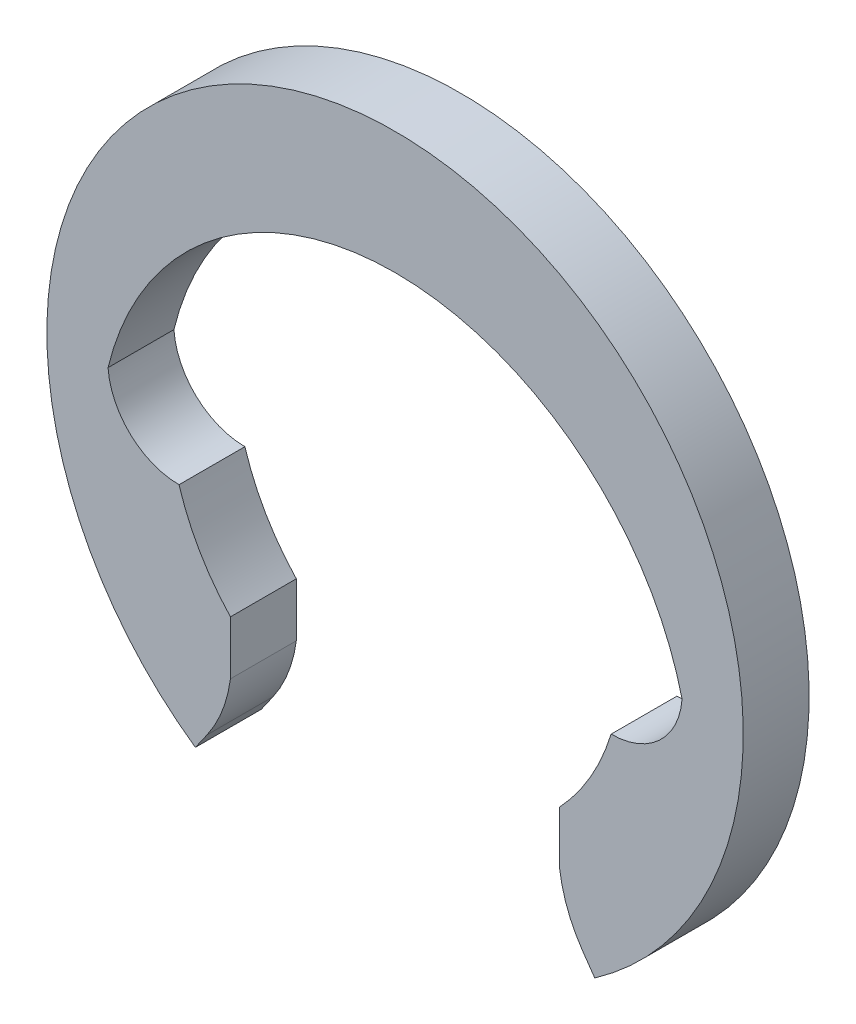
SolidWorks part; units mm, degrees
ref_plane "Front" through (0, 0, 0) normal (0, 0, 1) x (1, 0, 0)
ref_plane "Top" through (0, 0, 0) normal (0, 1, 0) x (1, 0, 0)
ref_plane "Right" through (0, 0, 0) normal (1, 0, 0) x (0, 0, -1)
sketch "Layout" plane through (0, 0, 0) normal (0, 0, 1) x (1, 0, 0)
  line L0 (0, 3.7) -> (0, -3.7) construction
  line L1 (-2.4, 0) -> (-3.7, 0) construction
  line L2 (-3.7, 0) -> (-4.4, 0) construction
  line L3 (-2.4, 0) -> (2.4, 0) construction
  line L4 (-1.7494, -2.4984) -> (-1.7494, -1.643) construction
  line L5 (-2.2956, -0.7) -> (2.2956, -0.7) construction
  line L6 (-2.4, 0) -> (-2.4, -0.7) construction
  line L7 (0, 0) -> (-1.3766, -1.966) construction
  line L8 (-1.3766, -1.966) -> (-2.1222, -3.0309) construction
  circle A0 centre (0, 0) radius 3.7 construction
  circle A1 centre (0, 0) radius 2.4 construction
  arc A2 (0, 2.4) -> (-3.05, 0) centre (0, -0.738) ccw construction
  circle A3 centre (0, 0) radius 3.8 construction
  arc A4 (-3.05, 0) -> (-2.2956, -0.7) centre (-2.2956, 0.0565) ccw construction
  dimension "D1" = 35
sketch "Sketch2" plane through (0, 0, 0) normal (0, 0, 1) x (1, 0, 0)
  line L0 (-1.7494, -2.4984) -> (-1.7494, -2.2133) construction
  line L1 (-1.7494, -2.2133) -> (-1.7494, -1.9282)
  line L2 (-1.7494, -1.9282) -> (-1.7494, -1.643)
  line L4 (0, 3.7) -> (0, -3.7) construction
  line L5 (-1.7494, -2.4984) -> (-1.8737, -2.6759) construction
  line L6 (0, 3.7) -> (0, 2.4) construction
  line L7 (-1.8737, -2.6759) -> (-1.998, -2.8534) construction
  line L8 (-1.998, -2.8534) -> (-2.1222, -3.0309)
  line L9 (-1.3766, -1.966) -> (-2.1222, -3.0309) construction
  line L10 (1.7494, -1.9282) -> (1.7494, -1.643)
  line L11 (1.7494, -2.2133) -> (1.7494, -1.9282)
  line L12 (1.998, -2.8534) -> (2.1222, -3.0309)
  circle A0 centre (0, 0) radius 3.7 construction
  arc A1 (0, 2.4) -> (-3.05, 0) centre (0, -0.738) ccw construction
  arc A2 (-3.05, 0) -> (-2.2956, -0.7) centre (-2.2956, 0.0565) ccw construction
  circle A3 centre (0, 0) radius 2.4 construction
  arc A4 (2.1222, -3.0309) -> (-2.1222, -3.0309) centre (0, 0) ccw
  arc A5 (3.05, 0) -> (-3.05, 0) centre (0, -0.738) ccw
  arc A6 (-3.05, 0) -> (-2.2956, -0.7) centre (-2.2956, 0.0565) ccw
  arc A7 (-2.2956, -0.7) -> (-1.7494, -1.643) centre (0, 0) ccw
  arc A8 (-1.7494, -2.2133) -> (-1.998, -2.8534) centre (-3.1788, -2.0266) cw
  arc A9 (1.7494, -2.2133) -> (1.998, -2.8534) centre (3.1788, -2.0266) ccw
  arc A10 (2.2956, -0.7) -> (1.7494, -1.643) centre (0, 0) cw
  arc A11 (3.05, 0) -> (2.2956, -0.7) centre (2.2956, 0.0565) cw
extrude "Boss-Extrude1" add sketch "Sketch2" along normal blind 0.7
equation "\"D1@Boss-Extrude1\"=\"thickness@Layout\""
